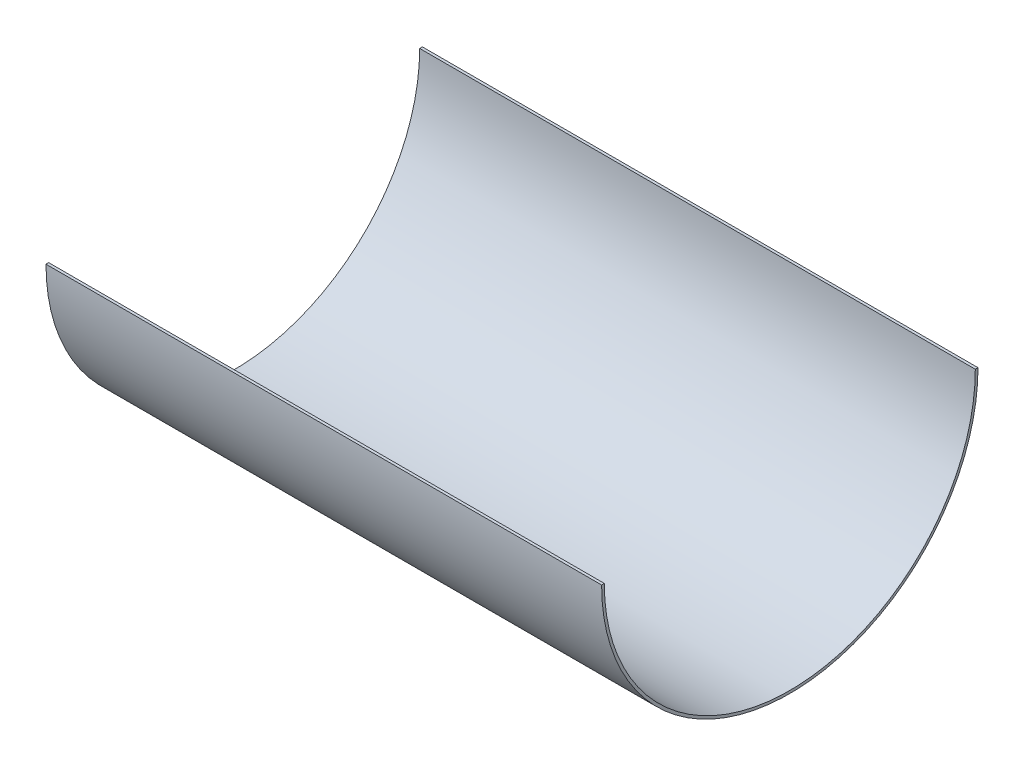
SolidWorks part; units mm, degrees
ref_plane "Front Plane" through (0, 0, 0) normal (0, 0, 1) x (1, 0, 0)
ref_plane "Top Plane" through (0, 0, 0) normal (0, 1, 0) x (1, 0, 0)
ref_plane "Right Plane" through (0, 0, 0) normal (1, 0, 0) x (0, 0, -1)
sketch "Sketch1" plane through (0, 0, 0) normal (0, 1, 0) x (1, 0, 0)
  line L0 (-38.4161, -102.436) -> (581.5839, -102.436)
  line L1 (-396.5921, -312.436) -> (1258.7695, -312.436) construction
  line L2 (-38.4161, -105.436) -> (581.5722, -105.436)
  line L3 (-148.4161, -297.436) -> (-145.4162, -297.4487)
  line L4 (688.5839, -232.436) -> (691.5839, -232.436)
  spline S0 degree 3 poles (-38.4161, -102.436) (-139.4449, -102.6441) (-148.3699, -286.573) (-148.4161, -297.436) knots 0 0 0 0 1 1 1 1
  spline S2 degree 3 poles (581.5839, -102.436) (693.4555, -103.3001) (691.5839, -210.8024) (691.5839, -232.436) knots 0 0 0 0 1 1 1 1
  spline S4 degree 3 poles (-145.4162, -297.4487) (-145.4158, -297.3631) (-145.4143, -297.2091) (-145.4065, -296.7636) (-145.3876, -296.059) (-145.3481, -294.9637) (-145.2705, -293.1962) (-145.1222, -290.4302) (-144.8469, -286.2922) (-144.4591, -281.402) (-143.772, -273.9673) (-142.5563, -263.1242) (-140.4063, -248.1593) (-137.4452, -231.7679) (-133.5543, -214.4771) (-128.6167, -196.8153) (-122.5183, -179.3119) (-115.1499, -162.4979) (-106.41, -146.9032) (-96.2071, -133.0523) (-86.418, -123.386) (-77.7696, -117.0141) (-70.8592, -112.9705) (-63.5047, -109.7164) (-56.9853, -107.7086) (-51.5204, -106.5542) (-47.2941, -105.9222) (-43.6595, -105.5972) (-40.6895, -105.4625) (-39.1712, -105.4376) (-38.4161, -105.436) knots 0.000021 0.000021 0.000021 0.000021 0.007833 0.015646 0.03127 0.046895 0.06252 0.093769 0.125019 0.156268 0.187517 0.250016 0.312515 0.375013 0.437512 0.500011 0.562509 0.625008 0.687507 0.750005 0.812504 0.843753 0.875003 0.906252 0.937501 0.953126 0.968751 0.984375 0.992188 1 1 1 1
  spline S5 degree 3 poles (581.5722, -105.436) (582.4242, -105.4426) (584.1379, -105.4689) (587.4841, -105.5715) (591.5711, -105.7929) (596.3076, -106.2026) (602.4091, -106.9348) (609.6394, -108.1867) (617.7059, -110.1905) (625.1867, -112.6593) (634.4142, -116.5233) (644.6121, -122.339) (654.9138, -130.6304) (663.4693, -139.982) (670.4504, -150.1415) (676.0167, -160.8476) (680.3233, -171.829) (683.5257, -182.807) (685.7821, -193.4984) (687.2534, -203.6189) (687.9614, -211.3398) (688.2994, -216.9475) (688.4596, -220.834) (688.5471, -224.3659) (688.5828, -227.5129) (688.5867, -229.7771) (688.5848, -231.3838) (688.5839, -232.076) (688.5839, -232.436) knots 0.000035 0.000035 0.000035 0.000035 0.007847 0.015659 0.031284 0.046908 0.062533 0.093782 0.125031 0.15628 0.187528 0.250026 0.312524 0.375022 0.43752 0.500017 0.562515 0.625013 0.687511 0.750009 0.812507 0.843755 0.875004 0.906253 0.937502 0.968751 0.984376 1 1 1 1
  dimension "D1" = 110
  dimension "D2" = 110
  dimension "D3" = 620
  dimension "D4" = 195
  dimension "D5" = 130
  dimension "D6" = 15
revolve "Revolve1" add sketch "Sketch1" angle 360 about L1
ref_plane "Plane1" through (-38.4161, 0, 0) normal (1, 0, 0) x (0, 0, -1)
ref_plane "Plane2" through (581.5839, 0, 0) normal (1, 0, 0) x (0, 0, -1)
sketch "Sketch4" plane through (-38.4161, 0, 0) normal (1, 0, 0) x (0, 0, -1)
  line L1 (-737.4959, 357.9485) -> (221.112, 357.9485)
  line L2 (-737.4959, 357.9485) -> (-737.4959, 0)
  line L3 (-737.4959, 0) -> (221.112, 0)
  line L4 (221.112, 357.9485) -> (221.112, 0)
extrude "Cut-Extrude2" cut sketch "Sketch4" along normal up to surface (620 mm away)
sketch "Sketch5" plane through (0, 0, 0) normal (0, 1, 0) x (1, 0, 0)
  line L0 (-38.4161, -115.5) -> (-38.4161, 115.5) construction
  line L1 (-386.8315, 104.3163) -> (-38.4161, 104.3163)
  line L2 (-386.8315, 104.3163) -> (-386.8315, -574.8437)
  line L3 (-386.8315, -574.8437) -> (-38.4161, -574.8437)
  line L4 (-38.4161, 104.3163) -> (-38.4161, -574.8437)
  line L5 (581.5839, -115.5) -> (581.5839, 115.5) construction
  line L6 (961.2602, -736.451) -> (581.5839, -736.451)
  line L7 (961.2602, -736.451) -> (961.2602, 122.7273)
  line L8 (961.2602, 122.7273) -> (581.5839, 122.7273)
  line L9 (581.5839, -736.451) -> (581.5839, 122.7273)
extrude "Cut-Extrude3" cut sketch "Sketch5" against normal mid plane 1000
